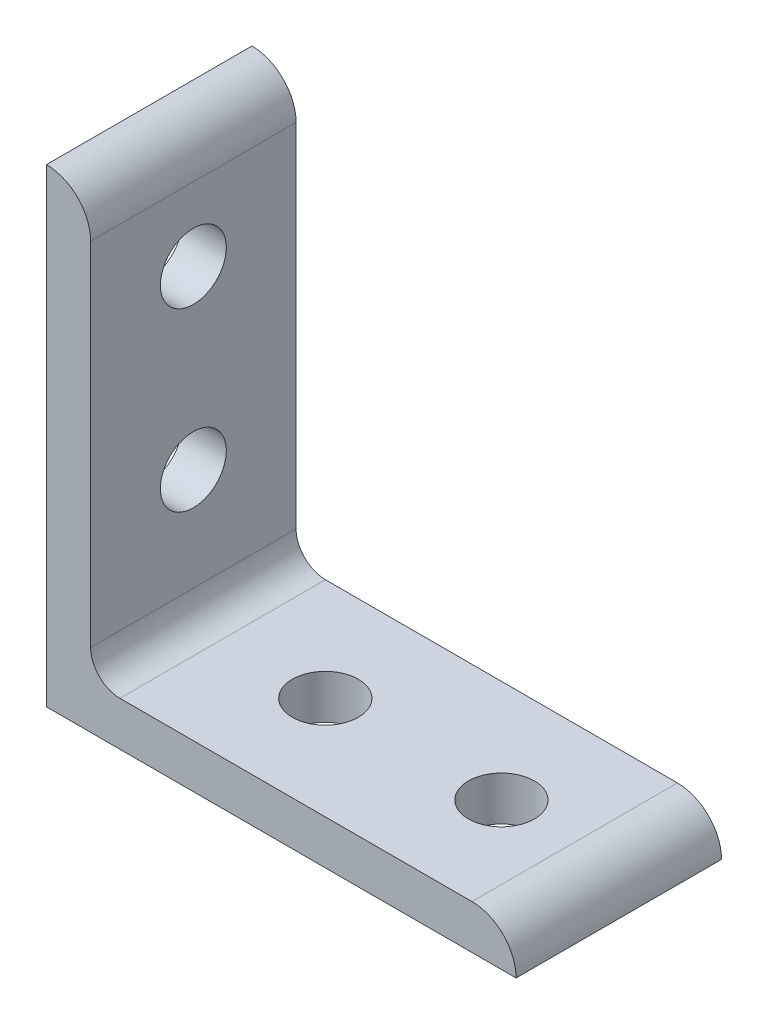
SolidWorks part; units mm, degrees
ref_plane "Front Plane" through (0, 0, 0) normal (0, 0, 1) x (1, 0, 0)
ref_plane "Top Plane" through (0, 0, 0) normal (0, 1, 0) x (1, 0, 0)
ref_plane "Right Plane" through (0, 0, 0) normal (1, 0, 0) x (0, 0, -1)
sketch "Sketch1" plane through (0, 0, 0) normal (0, 0, 1) x (1, 0, 0)
  line L0 (0, 0) -> (0, 50.8)
  line L1 (4.7752, 46.0248) -> (4.7752, 50.8) construction
  line L2 (4.7752, 46.0248) -> (4.7752, 7.9502)
  line L3 (7.9502, 4.7752) -> (46.0248, 4.7752)
  line L4 (4.7752, 50.8) -> (0, 50.8) construction
  line L5 (50.8, 0) -> (0, 0)
  line L6 (46.0248, 4.7752) -> (50.8, 4.7752) construction
  line L7 (50.8, 4.7752) -> (50.8, 0) construction
  arc A0 (4.7752, 46.0248) -> (0, 50.8) centre (0, 46.0248) ccw
  arc A1 (50.8, 0) -> (46.0248, 4.7752) centre (46.0248, 0) ccw
  arc A2 (4.7752, 7.9502) -> (7.9502, 4.7752) centre (7.9502, 7.9502) ccw
  point P10 (4.7752, 48.4124)
  dimension "E" = 3.175
  dimension "D" = 4.7752
  dimension "C" = 50.8
  dimension "B" = 50.8
extrude "Boss-Extrude1" add sketch "Sketch1" along normal mid plane 22.225
sketch "Sketch2" plane through (0, 0, 0) normal (0, 1, 0) x (1, 0, 0)
  line L0 (0, 0) -> (19.05, 0) construction
  line L1 (19.05, 0) -> (38.1, 0) construction
  circle A0 centre (19.05, 0) radius 3.5687
  circle A1 centre (38.1, 0) radius 3.5687
extrude "Cut-Extrude1" cut sketch "Sketch2" along normal through all
sketch "Sketch3" plane through (0, 0, 0) normal (1, 0, 0) x (0, 0, -1)
  line L0 (0, 0) -> (0, 19.05) construction
  line L1 (0, 19.05) -> (0, 38.1) construction
  circle A0 centre (0, 19.05) radius 3.5687
  circle A1 centre (0, 38.1) radius 3.5687
  dimension "D1" = 19.05
  dimension "D2" = 19.05
extrude "Cut-Extrude2" cut sketch "Sketch3" along normal through all
equation "\"E@Sketch3\" = \"E@Sketch2\""
equation "\"D1@Sketch3\" = \"D1@Sketch2\""
equation "\"D2@Sketch3\" = \"D2@Sketch2\""
